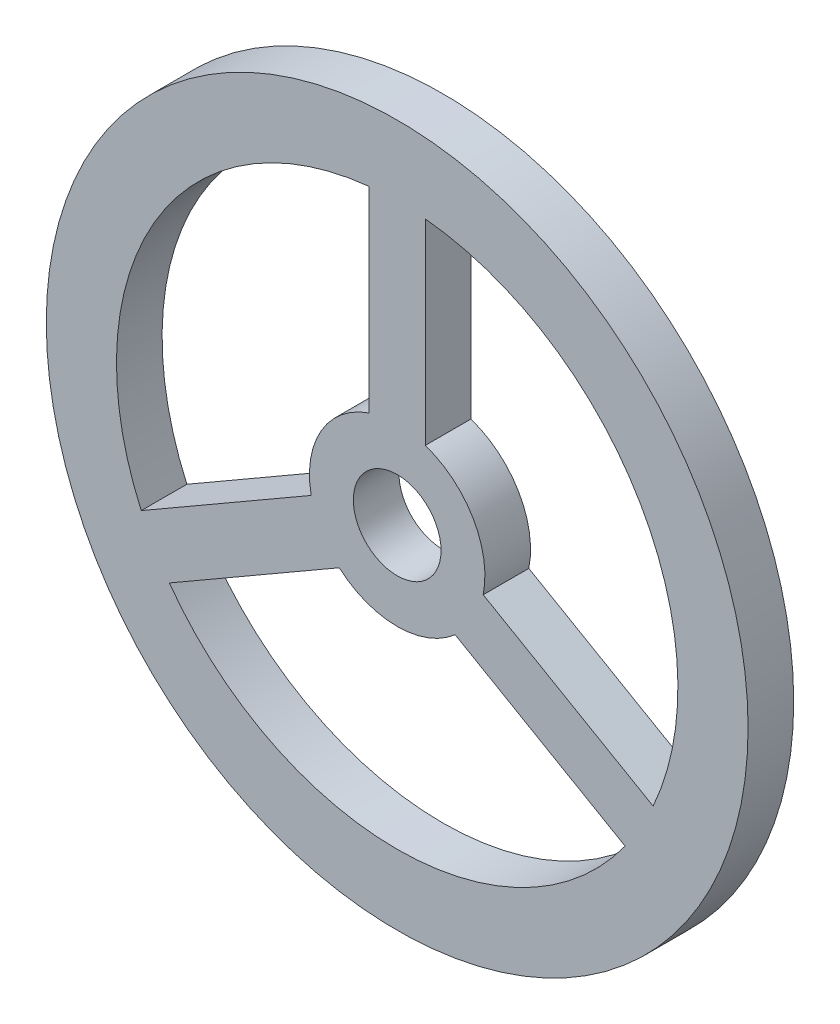
SolidWorks part; units mm, degrees
material "AISI 304"
ref_plane "Plan de face" through (0, 0, 0) normal (0, 0, 1) x (1, 0, 0)
ref_plane "Plan de dessus" through (0, 0, 0) normal (0, 1, 0) x (1, 0, 0)
ref_plane "Plan de droite" through (0, 0, 0) normal (1, 0, 0) x (0, 0, -1)
sketch "Esquisse1" plane through (0, 0, 0) normal (0, 0, 1) x (1, 0, 0)
  circle A0 centre (0, 0) radius 10
  dimension "D1" = 20
extrude "base" add sketch "Esquisse1" along normal blind 1.3
sketch "Esquisse2" plane through (0, 0, 1.3) normal (0, 0, 1) x (1, 0, 0)
  line L0 (0, 0) -> (0, 22.2884) construction
  line L1 (0, 0) -> (-20.1905, -11.657) construction
  line L2 (0, 0) -> (15.8132, -9.1297) construction
  line L3 (-20.5539, -10.943) -> (-2.4512, -0.4915) construction
  line L4 (-19.7433, -12.3226) -> (-1.6512, -1.8771) construction
  line L5 (-7.2935, -3.2871) -> (-2.4512, -0.4915)
  line L6 (-6.4935, -4.6728) -> (-1.6512, -1.8771)
  line L7 (1.6512, -1.8771) -> (15.4423, -9.8394) construction
  line L8 (16.1798, -8.4177) -> (2.4512, -0.4915) construction
  line L9 (6.4935, -4.6728) -> (1.6512, -1.8771)
  line L10 (2.4512, -0.4915) -> (7.2935, -3.2871)
  line L11 (0.8, 22.2884) -> (0.8, 2.3685) construction
  line L12 (-0.8, 2.3685) -> (-0.8, 22.2884) construction
  line L13 (-0.8, 7.9599) -> (-0.8, 2.3685)
  line L14 (0.8, 2.3685) -> (0.8, 7.9599)
  arc A0 (-6.4935, -4.6728) -> (6.4935, -4.6728) centre (0, 0) ccw
  arc A1 (-1.6512, -1.8771) -> (1.6512, -1.8771) centre (0, 0) ccw
  arc A2 (2.4512, -0.4915) -> (0.8, 2.3685) centre (0, 0) ccw
  arc A3 (7.2935, -3.2871) -> (0.8, 7.9599) centre (0, 0) ccw
  arc A4 (-0.8, 7.9599) -> (-7.2935, -3.2871) centre (0, 0) ccw
  arc A5 (-0.8, 2.3685) -> (-2.4512, -0.4915) centre (0, 0) ccw
  point P1 (2.7034, -0.6371)
  point P8 (-1.3269, -1.8771)
  point P10 (0, 0)
  point P16 (-20.5539, -10.943)
  point P22 (-0.8, 2.6818)
  point P23 (-2.1958, -0.4915)
  point P29 (-0.8, 22.2884)
  point P30 (0.8, 22.2884)
  point P31 (0, 22.2884)
  point P32 (-20.6918, -11.0226)
  point P33 (-20.1905, -11.657)
  point P34 (-20.1905, -12.5501)
  point P35 (0, 0)
  point P36 (4.4057, 3.4674)
  point P37 (5.5388, 2.3685)
  point P38 (4.6525, 3.6099)
  point P39 (-0.8, 1.2803)
  point P40 (0.8, -0.4619)
  point P41 (0.8808, 2.3397)
  point P42 (-19.7433, -12.3226)
  point P43 (15.4423, -9.8394)
  point P44 (16.1798, -8.4177)
  dimension "D1" = 120
  dimension "D9" = 8
  dimension "D10" = 2.5
  dimension "D2" = 120
  dimension "D3" = 0.8
  dimension "D4" = 0.8
  dimension "D5" = 0.8
  dimension "D6" = 0.8
  dimension "D7" = 0.8
  dimension "D8" = 0.8
extrude "holes" cut sketch "Esquisse2" against normal through all
sketch "Esquisse3" plane through (0, 0, 1.3) normal (0, 0, 1) x (1, 0, 0)
  circle A0 centre (0, 0) radius 1.25
  dimension "D1" = 2.5
extrude "hole_to_stirrer_bar" cut sketch "Esquisse3" against normal through all
